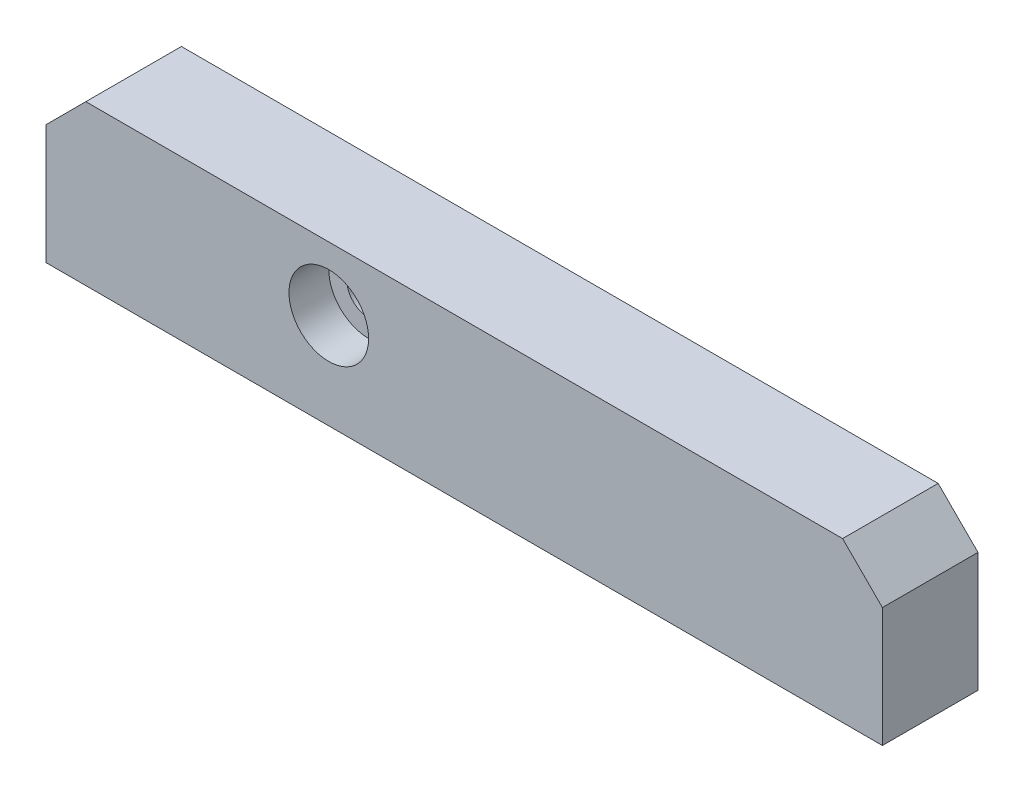
SolidWorks part; units mm, degrees
ref_plane "Front" through (0, 0, 0) normal (0, 0, 1) x (1, 0, 0)
ref_plane "Top" through (0, 0, 0) normal (0, 1, 0) x (1, 0, 0)
ref_plane "Right" through (0, 0, 0) normal (1, 0, 0) x (0, 0, -1)
sketch "Sketch1" plane through (0, 0, 0) normal (0, 0, 1) x (1, 0, 0)
  line L0 (0, 30.4977) -> (0, -12.7362) construction
  line L1 (-47.5, 20) -> (-52.5, 15)
  line L2 (-52.5, 0) -> (52.5, 0)
  line L3 (-52.5, 0) -> (-52.5, 15)
  line L4 (-47.5, 20) -> (47.5, 20)
  line L5 (52.5, 0) -> (52.5, 15)
  line L6 (47.5, 20) -> (52.5, 15)
  dimension "D1" = 105
  dimension "D2" = 20
  dimension "D3" = 5
  dimension "D4" = 15
extrude "Boss-Extrude1" add sketch "Sketch1" along normal blind 12
hole_wizard "CBORE for M5 Socket Head Cap Screw1" positions "Sketch3" profile "Sketch2" counterbore size "M5" standard "JIS" end condition through all
sketch "Sketch3" plane through (0, 0, 12) normal (0, 0, 1) x (1, 0, 0)
  line L0 (-52.5, 15) -> (-52.5, 0) construction
  line L1 (-52.5, 0) -> (52.5, 0) construction
  point P0 (-17, 12)
  dimension "D1" = 35.5
  dimension "D2" = 12
sketch "Sketch2" plane through (-17, 12, 12) normal (1, 0, 0) x (0, -1, 0)
  line L0 (0, 0) -> (0, 12)
  line L1 (0, 12) -> (2.75, 12)
  line L3 (2.75, 12) -> (2.75, 5)
  line L4 (2.75, 5) -> (5, 5)
  line L5 (5, 5) -> (5, 0)
  line L7 (5, 0) -> (0, 0)
  line L11 (0, -6.35) -> (0, 107.95) construction
  dimension "通し穴の直径" = 5.5
  dimension "通し穴の深さ" = 12
  dimension "座ぐり穴の直径" = 10
  dimension "座ぐり穴の深さ" = 5
hole_wizard "M5x0.8 Tapped Hole1" positions "Sketch5" profile "Sketch4" tap size "M5x0.8" standard "JIS"
sketch "Sketch5" plane through (0, 0, 0) normal (0, -1, 0) x (1, 0, 0)
  line L1 (-52.5, 0) -> (52.5, 0) construction
  line L2 (0, 16.0581) -> (0, -5.4927) construction
  point P0 (-37.5, 6)
  point P1 (37.5, 6)
  dimension "D2" = 75
  dimension "D3" = 6
sketch "Sketch4" plane through (-37.5, 0, 6) normal (1, 0, 0) x (0, 0, -1)
  line L0 (0, 0) -> (0, 15.2618)
  line L1 (0, 15.2618) -> (2.1, 14)
  line L2 (2.1, 14) -> (2.1, 0)
  line L5 (2.1, 0) -> (0, 0)
  line L10 (0, 15.2618) -> (-2.1, 14) construction
  line L11 (0, -6.35) -> (0, 107.95) construction
  dimension "ねじ下穴ﾄﾞﾘﾙ直径" = 4.2
  dimension "ねじ下穴ﾄﾞﾘﾙの深さ" = 14
  dimension "ﾄﾞﾘﾙ角度" = 118
cosmetic thread "Hole Thread1" parameters "D1"=10, "D2"=5
cosmetic thread "Hole Thread2" parameters "D1"=10, "D2"=5
